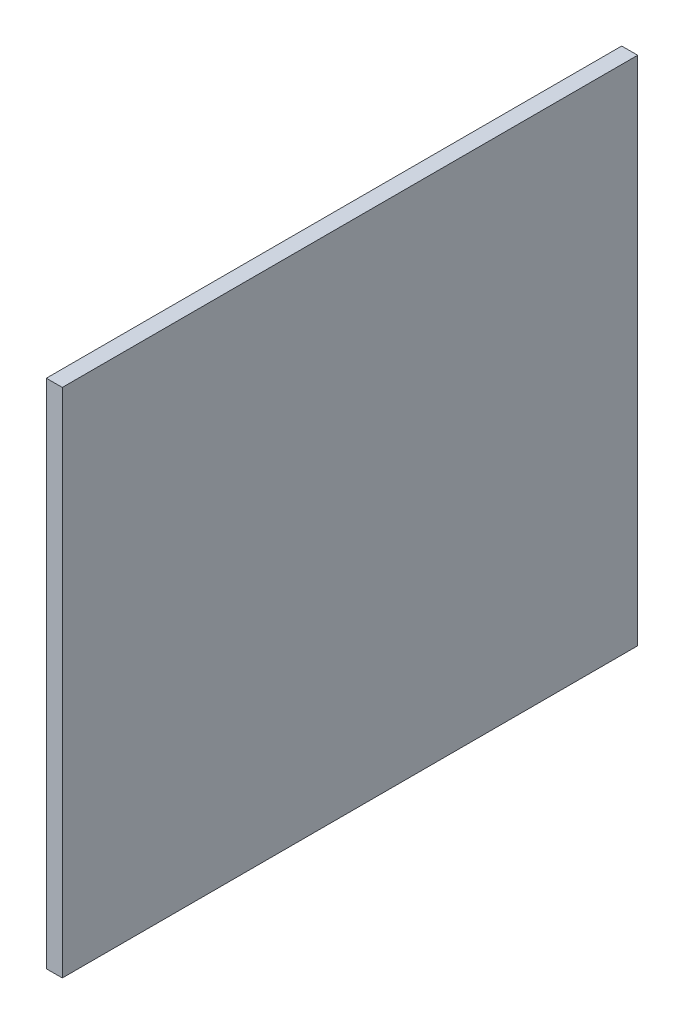
SolidWorks part; units mm, degrees
ref_plane "Front Plane" through (0, 0, 0) normal (0, 0, 1) x (1, 0, 0)
ref_plane "Top Plane" through (0, 0, 0) normal (0, 1, 0) x (1, 0, 0)
ref_plane "Right Plane" through (0, 0, 0) normal (1, 0, 0) x (0, 0, -1)
sketch "Sketch1" plane through (0, 0, 0) normal (1, 0, 0) x (0, 0, -1)
  line L1 (114.3, 101.6) -> (-114.3, 101.6)
  line L2 (114.3, 101.6) -> (114.3, -101.6)
  line L3 (114.3, -101.6) -> (-114.3, -101.6)
  line L4 (-114.3, 101.6) -> (-114.3, -101.6)
  line L5 (114.3, 101.6) -> (-114.3, -101.6) construction
  line L6 (114.3, -101.6) -> (-114.3, 101.6) construction
  point P0 (0, 0)
  dimension "D1" = 203.2
  dimension "D2" = 228.6
extrude "Boss-Extrude1" add sketch "Sketch1" along normal blind 6.35
